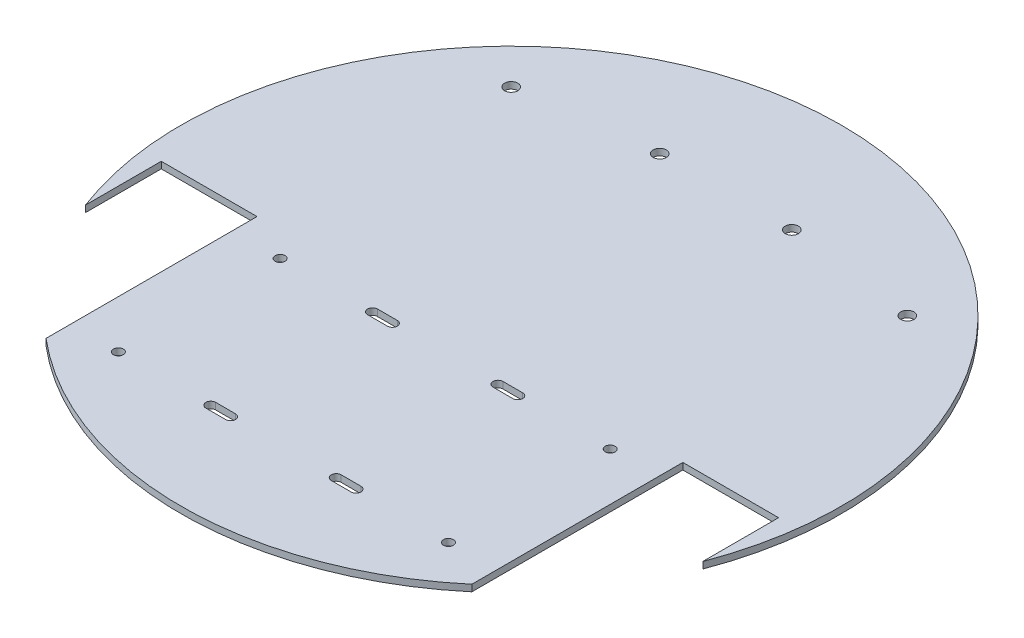
SolidWorks part; units mm, degrees
ref_plane "Front Plane" through (0, 0, 0) normal (0, 0, 1) x (1, 0, 0)
ref_plane "Top Plane" through (0, 0, 0) normal (0, 1, 0) x (1, 0, 0)
ref_plane "Right Plane" through (0, 0, 0) normal (1, 0, 0) x (0, 0, -1)
sketch "Sketch1" plane through (0, 0, 0) normal (0, 1, 0) x (1, 0, 0)
  line L0 (0, 107.5512) -> (0, -106.9432) construction
  line L1 (-159.5954, 0) -> (140.6967, 0) construction
  line L2 (-50, 39.3685) -> (-50, -79.3685) construction
  line L3 (-77.1985, -44.5) -> (15.3752, -44.5) construction
  line L4 (-34.5, -1.9111) -> (-34.5, -79.3685) construction
  line L5 (-16, -20) -> (-22, -20) construction
  line L6 (-16, -21.5) -> (-22, -21.5)
  line L7 (-16, -18.5) -> (-22, -18.5)
  line L8 (-16, -69) -> (-22, -69) construction
  line L9 (-16, -67.5) -> (-22, -67.5)
  line L10 (-16, -70.5) -> (-22, -70.5)
  line L11 (16, -20) -> (22, -20) construction
  line L12 (16, -21.5) -> (22, -21.5)
  line L13 (16, -18.5) -> (22, -18.5)
  line L14 (16, -69) -> (22, -69) construction
  line L15 (16, -67.5) -> (22, -67.5)
  line L16 (16, -70.5) -> (22, -70.5)
  line L17 (-64.5, 38.8079) -> (-64.5, -103.4684) construction
  line L18 (-93.5, 38.8079) -> (-93.5, -35.4648) construction
  line L19 (-93.5, -12.5) -> (-64.5, -12.5)
  line L20 (-64.5, -12.5) -> (-64.5, -76.5)
  line L21 (-93.5, -12.5) -> (-93.5, -35.4648)
  line L23 (93.5, -12.5) -> (64.5, -12.5)
  line L24 (64.5, -12.5) -> (64.5, -76.5)
  line L26 (93.5, -12.5) -> (93.5, -35.4648)
  arc A0 (-64.5, -76.4183) -> (64.5, -76.4183) centre (0, 0) ccw
  circle A1 centre (-50, -20) radius 1.5
  arc A2 (-16, -67.5) -> (-16, -70.5) centre (-16, -69) cw
  arc A3 (-22, -70.5) -> (-22, -67.5) centre (-22, -69) cw
  circle A4 centre (-50, -69) radius 1.5
  arc A5 (-16, -21.5) -> (-16, -18.5) centre (-16, -20) ccw
  arc A6 (-22, -18.5) -> (-22, -21.5) centre (-22, -20) ccw
  arc A7 (16, -21.5) -> (16, -18.5) centre (16, -20) cw
  arc A8 (22, -18.5) -> (22, -21.5) centre (22, -20) cw
  arc A9 (16, -67.5) -> (16, -70.5) centre (16, -69) ccw
  arc A10 (22, -70.5) -> (22, -67.5) centre (22, -69) ccw
  circle A11 centre (50, -69) radius 1.5
  circle A12 centre (50, -20) radius 1.5
  arc A13 (93.5, -35.4648) -> (-93.5, -35.4648) centre (0, 0) ccw
  circle A14 centre (-20, 65) radius 2
  circle A15 centre (20, 65) radius 2
  circle A16 centre (-60, 60) radius 2
  circle A17 centre (60, 60) radius 2
  point P9 (-19, -69)
  point P23 (-19, -20)
  point P33 (19, -20)
  point P40 (19, -69)
  point P58 (-64.5, -44.5)
  point P59 (-93.5, -44.5)
  dimension "D1" = 200
  dimension "D6" = 3
  dimension "D4" = 29
  dimension "D11" = 4
  dimension "D14" = 4
  dimension "D2" = 6
  dimension "D3" = 3
  dimension "D5" = 31
  dimension "D7" = 14.5
  dimension "D8" = 32
  dimension "D9" = 50
  dimension "D10" = 44.5
  dimension "D12" = 20
  dimension "D13" = 65
  dimension "D15" = 60
  dimension "D16" = 60
extrude "Boss-Extrude1" add sketch "Sketch1" along normal blind 2 contours L26 A13 L21 L19 L20 A0 L24 L23 A12 A11 A10 L16 A9 L15 A6 L7 A5 L6 L10 A3 L9 A2 A1 A4 L13 A8 L12 A7
